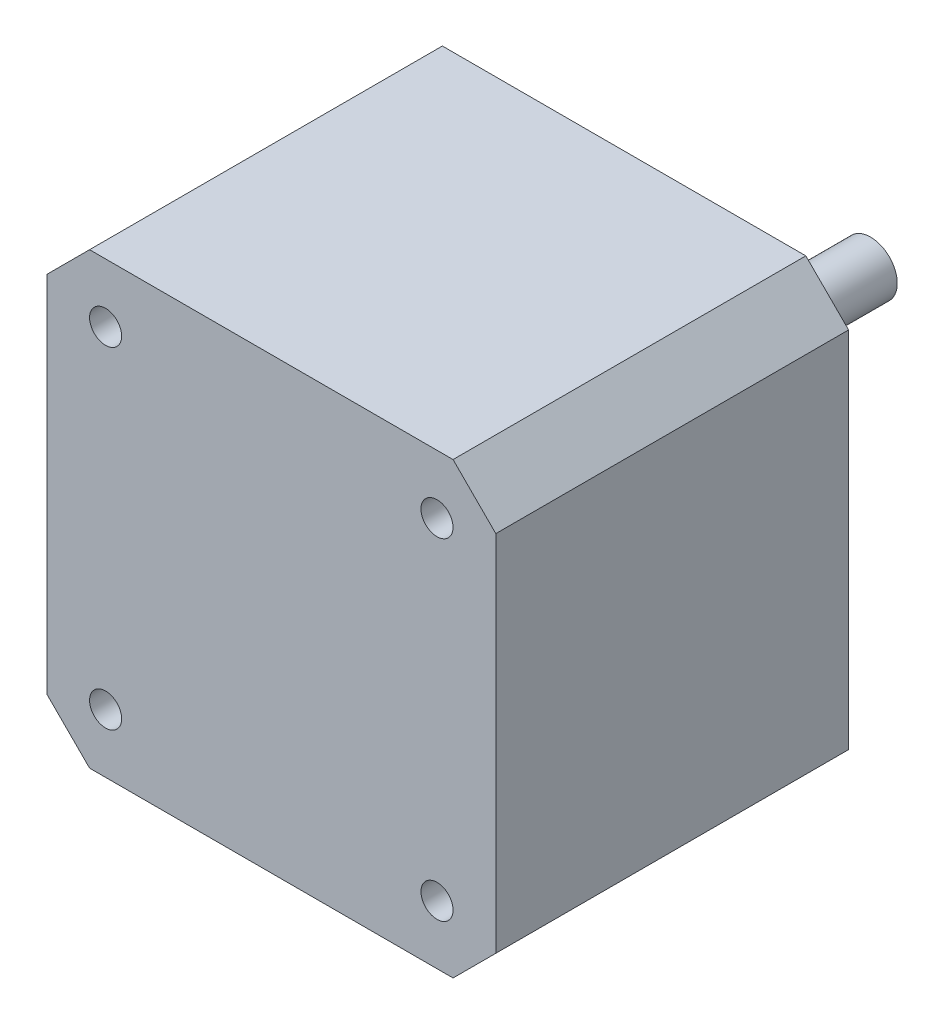
SolidWorks part; units mm, degrees
ref_plane "Przednia" through (0, 0, 0) normal (0, 0, 1) x (1, 0, 0)
ref_plane "Górna" through (0, 0, 0) normal (0, 1, 0) x (1, 0, 0)
ref_plane "Prawa" through (0, 0, 0) normal (1, 0, 0) x (0, 0, -1)
sketch "Szkic1" plane through (0, 0, 0) normal (0, 0, 1) x (1, 0, 0)
  line L1 (-21, -21) -> (21, -21)
  line L2 (-21, -21) -> (-21, 21)
  line L3 (-21, 21) -> (21, 21)
  line L4 (21, -21) -> (21, 21)
  line L5 (-21, -21) -> (21, 21) construction
  line L6 (-21, 21) -> (21, -21) construction
  point P0 (0, 0)
  dimension "D1" = 42
extrude "Dodanie-wyciągnięcie1" add sketch "Szkic1" along normal blind 33
chamfer "Sfazowanie1" distance 4 angle 45 4 edges at (-21, -21, 16.5) (21, -21, 16.5) (-21, 21, 16.5) (21, 21, 16.5)
sketch "Szkic2" plane through (0, 0, 0) normal (0, 0, -1) x (-1, 0, 0)
  circle A0 centre (0, 0) radius 11
  dimension "D1" = 22
extrude "Dodanie-wyciągnięcie2" add sketch "Szkic2" along normal blind 1.3
sketch "Szkic3" plane through (0, 0, -1.3) normal (0, 0, -1) x (-1, 0, 0)
  circle A0 centre (0, 0) radius 2.5
  dimension "D1" = 5
extrude "Dodanie-wyciągnięcie3" add sketch "Szkic3" along normal blind 21.75
sketch "Szkic4" plane through (0, 0, 0) normal (0, 0, -1) x (-1, 0, 0)
  line L0 (0, -23.3741) -> (0, 23.3741) construction
  line L1 (0, 0) -> (30.3505, 0) construction
  circle A0 centre (15.5, 15.5) radius 1.5
  circle A1 centre (-15.5, 15.5) radius 1.5
  circle A2 centre (-15.5, -15.5) radius 1.5
  circle A3 centre (15.5, -15.5) radius 1.5
  dimension "D2" = 3
  dimension "D1" = 31
  dimension "D3" = 31
extrude "Wytnij-wyciągnięcie1" cut sketch "Szkic4" against normal through all
equation "\"D3@Szkic4\"=\"D1@Szkic4\""
